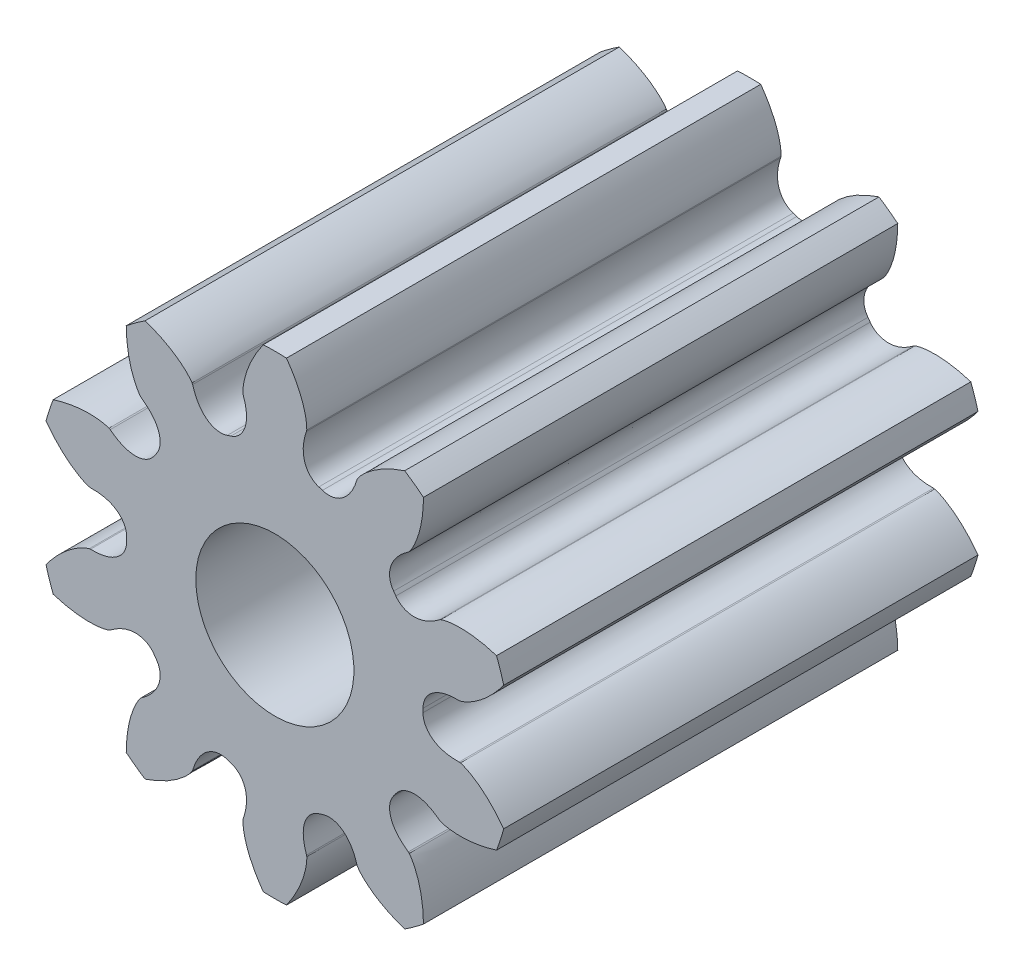
SolidWorks part; units mm, degrees
ref_plane "Front Plane" through (0, 0, 0) normal (0, 0, 1) x (1, 0, 0)
ref_plane "Top Plane" through (0, 0, 0) normal (0, 1, 0) x (1, 0, 0)
ref_plane "Right Plane" through (0, 0, 0) normal (1, 0, 0) x (0, 0, -1)
sketch "Pitch Diameter" plane through (0, 0, 0) normal (0, 0, 1) x (1, 0, 0)
  circle A0 centre (0, 0) radius 2.5
  dimension "D1" = 5
sketch "Sketch1" plane through (0, 0, 0) normal (0, 0, 1) x (1, 0, 0)
  line L0 (0.4038, 2.337) -> (0.4008, 2.3209)
  line L1 (0, 3.1774) -> (0, 0) construction
  line L2 (0, 0) -> (0, 3.1774) construction
  line L3 (-0.4038, 2.337) -> (-0.4008, 2.3209)
  arc A0 (-0.5564, 1.7905) -> (0.5564, 1.7905) centre (0, 0) ccw
  spline S0 degree 3 poles (0, 3.1774) (0.0678, 3.1029) (0.1575, 2.9894) (0.2528, 2.8331) (0.3056, 2.7295) (0.3448, 2.6351) (0.3723, 2.5513) (0.39, 2.4792) (0.4015, 2.4093) (0.4046, 2.3631) (0.4038, 2.337) knots 0 0 0 0 0.317754 0.454552 0.576631 0.68399 0.776631 0.854552 0.917754 1 1 1 1
  spline S1 degree 3 poles (0.4008, 2.3209) (0.3867, 2.2821) (0.3701, 2.2234) (0.3595, 2.1443) (0.3579, 2.087) (0.3631, 2.0303) (0.3766, 1.9738) (0.4004, 1.9179) (0.4514, 1.8443) (0.5107, 1.8045) (0.5564, 1.7905) knots 0 0 0 0 0.200126 0.294348 0.386168 0.477231 0.569745 0.66645 0.770113 1 1 1 1
  spline S2 degree 3 poles (-0.4008, 2.3209) (-0.3867, 2.2821) (-0.3701, 2.2234) (-0.3595, 2.1443) (-0.3579, 2.087) (-0.3631, 2.0303) (-0.3766, 1.9738) (-0.4004, 1.9179) (-0.4514, 1.8443) (-0.5107, 1.8045) (-0.5564, 1.7905) knots 0 0 0 0 0.200126 0.294348 0.386168 0.477231 0.569745 0.66645 0.770113 1 1 1 1
  spline S3 degree 3 poles (0, 3.1774) (-0.0678, 3.1029) (-0.1575, 2.9894) (-0.2528, 2.8331) (-0.3056, 2.7295) (-0.3448, 2.6351) (-0.3723, 2.5513) (-0.39, 2.4792) (-0.4015, 2.4093) (-0.4046, 2.3631) (-0.4038, 2.337) knots 0 0 0 0 0.317754 0.454552 0.576631 0.68399 0.776631 0.854552 0.917754 1 1 1 1
  point P2 (0, 3.1774)
  point P4 (0.102, 3.0565)
  point P5 (0.1861, 2.9395)
  point P6 (0.2537, 2.8283)
  point P7 (0.3062, 2.7247)
  point P8 (0.3453, 2.6303)
  point P9 (0.3726, 2.5465)
  point P10 (0.3901, 2.4745)
  point P11 (0.3997, 2.4151)
  point P12 (0.4036, 2.3691)
  point P13 (0.4038, 2.337)
  point P14 (0.4008, 2.3209)
  point P15 (0.3815, 2.2606)
  point P18 (0.368, 2.2016)
  point P19 (0.3604, 2.1437)
  point P20 (0.359, 2.0869)
  point P21 (0.3644, 2.0308)
  point P22 (0.3779, 1.9751)
  point P23 (0.4016, 1.9202)
  point P24 (0.4383, 1.8676)
  point P25 (0.4905, 1.822)
  point P26 (0.5564, 1.7905)
other "AlignGroup4" parameters "D1"=14.359, "D2"=4.3343, "D3"=15.4996, "D4"=22.2419, "D5"=0.2537, "D6"=0.3062, "D7"=0.3453, "D8"=0.3726, "D9"=0.3901, "D10"=0.3997, "D11"=0.4036, "D12"=0.4038, "D13"=0.4008, "D14"=0.3815, "D15"=0.368, "D16"=0.3604, "D17"=0.359, "D18"=0.3644, "D19"=0.3779, "D20"=0.4016, "D21"=0.4383, "D22"=0.4905, "D23"=0.5564, "D24"=0, "D25"=3.1774, "D26"=3.0565, "D27"=2.9395, "D28"=2.8283, "D29"=2.7247, "D30"=2.6303, "D31"=2.5465, "D32"=2.4745, "D33"=2.4151, "D34"=2.3691, "D35"=2.337, "D36"=2.3209, "D37"=2.2606, "D38"=2.2016, "D39"=2.1437, "D40"=2.0869, "D41"=2.0308, "D42"=1.9751, "D43"=1.9202, "D44"=1.8676, "D45"=1.822, "D46"=1.7905
other "AlignGroup5"
extrude "Tooth" add sketch "Sketch1" along normal blind 6
pattern_circular "Teeth" count 10 over 360 about axis through (0, 0, 6) along (0, 0, -1) of "Tooth"
sketch "Sketch6" plane through (0, 0, 0) normal (0, 0, 1) x (1, 0, 0)
  circle A0 centre (0, 0) radius 3
  dimension "D1" = 6
extrude "Addendum" cut sketch "Sketch6" along normal through all flip side to cut
sketch "Sketch8" plane through (0, 0, 0) normal (0, 0, -1) x (-1, 0, 0)
  circle A0 centre (0, 0) radius 1
extrude "Cut-Extrude1" cut sketch "Sketch8" against normal through all
sketch "Sketch9" plane through (0, 0, 0) normal (0, 0, -1) x (-1, 0, 0)
